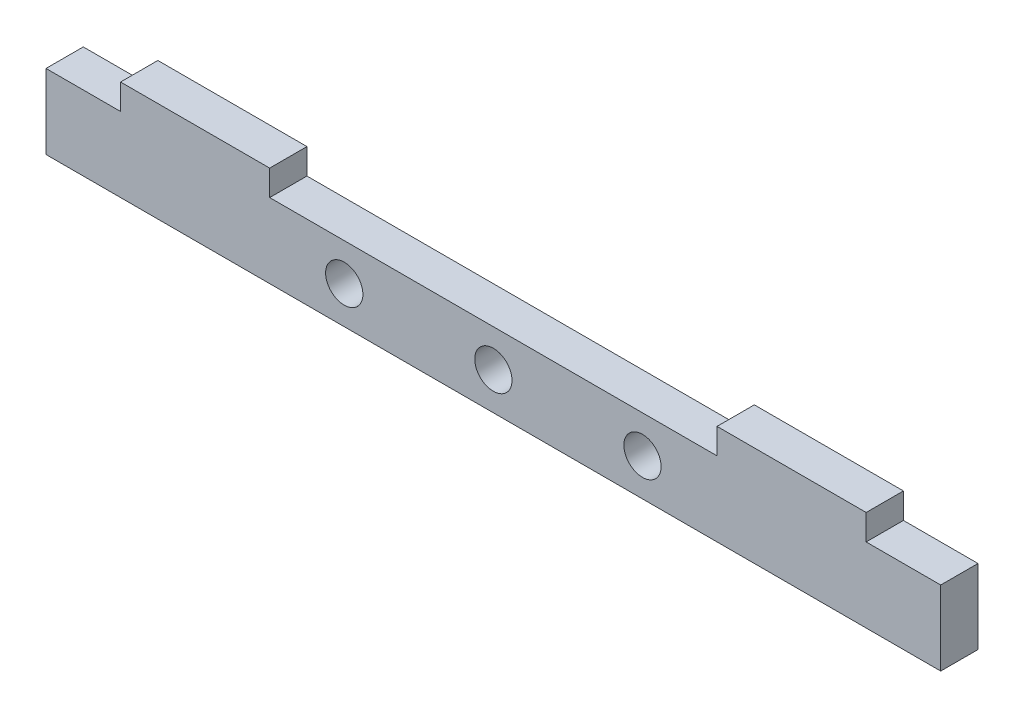
SolidWorks part; units mm, degrees
ref_plane "Front Plane" through (0, 0, 0) normal (0, 0, 1) x (1, 0, 0)
ref_plane "Top Plane" through (0, 0, 0) normal (0, 1, 0) x (1, 0, 0)
ref_plane "Right Plane" through (0, 0, 0) normal (1, 0, 0) x (0, 0, -1)
sketch "Sketch1" plane through (0, 0, 0) normal (0, 0, 1) x (1, 0, 0)
  line L0 (38.1, 12.7) -> (114.3, 12.7)
  line L1 (0, 0) -> (152.4, 0)
  line L2 (0, 0) -> (0, 12.7)
  line L3 (0, 12.7) -> (12.7, 12.7)
  line L4 (152.4, 0) -> (152.4, 12.7)
  line L6 (12.7, 12.7) -> (12.7, 17.0502)
  line L7 (12.7, 17.0502) -> (38.1, 17.0502)
  line L8 (38.1, 12.7) -> (38.1, 17.0502)
  line L10 (114.3, 12.7) -> (114.3, 17.0502)
  line L11 (139.7, 17.0502) -> (114.3, 17.0502)
  line L12 (139.7, 12.7) -> (139.7, 17.0502)
  line L13 (139.7, 12.7) -> (152.4, 12.7)
  circle A0 centre (50.8, 6.35) radius 3.175
  circle A1 centre (76.2, 6.35) radius 3.175
  circle A2 centre (101.6, 6.35) radius 3.175
  dimension "D1" = 25.4
  dimension "D2" = 12.7
extrude "Boss-Extrude1" add sketch "Sketch1" along normal blind 6.35
